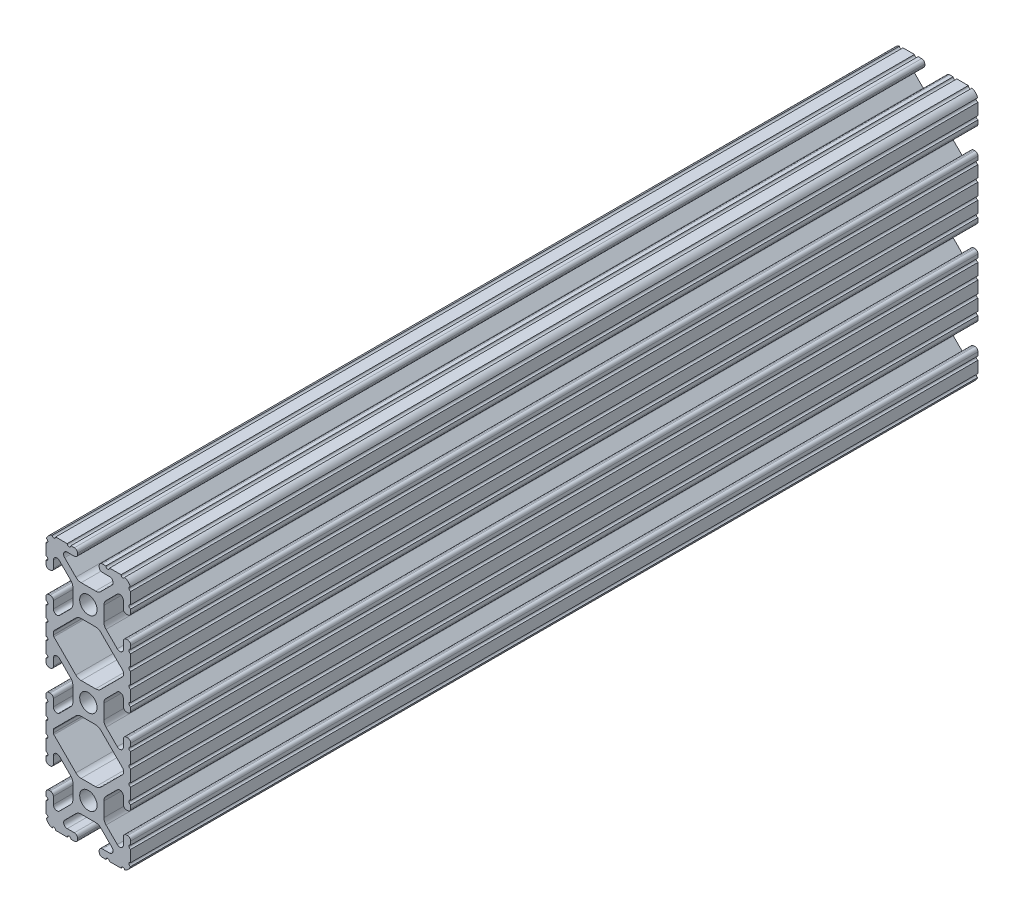
SolidWorks part; units mm, degrees
material "6061-T6 (SS)"
ref_plane "Front Plane" through (0, 0, 0) normal (0, 0, 1) x (1, 0, 0)
ref_plane "Top Plane" through (0, 0, 0) normal (0, 1, 0) x (1, 0, 0)
ref_plane "Right Plane" through (0, 0, 0) normal (1, 0, 0) x (0, 0, -1)
sketch "Sketch2" plane through (0, 0, 0) normal (0, 0, 1) x (1, 0, 0)
  line L0 (0, 38.1) -> (0, -38.1) construction
  line L1 (-12.7, 0) -> (12.7, 0) construction
  line L2 (3.2512, -38.1) -> (12.7, -38.1)
  line L3 (12.7, -38.1) -> (12.7, -28.6512)
  line L4 (3.2512, -38.1) -> (3.2512, -35.8902)
  line L5 (3.2512, -35.8902) -> (8.9276, -35.8902)
  line L6 (8.9276, -35.8902) -> (3.0856, -30.0482)
  line L7 (0, -25.4) -> (12.7, -38.1) construction
  line L8 (12.7, -28.6512) -> (10.4902, -28.6512)
  line L9 (10.4902, -28.6512) -> (10.4902, -34.3276)
  line L10 (10.4902, -34.3276) -> (4.6482, -28.4856)
  circle A0 centre (0, -25.4) radius 2.6035
  arc A1 (6.3485, -35.8902) -> (7.1039, -34.0665) centre (6.3485, -34.8219) ccw construction
  point P8 (0, -30.0482)
  dimension "Center Hole Diameter" = 5.207
  dimension "Rail Height" = 76.2
  dimension "Rail Width" = 25.4
  dimension "T-Slot Width" = 6.5024
  dimension "Slot Inner Width" = 14.8336
  dimension "Thickness" = 2.2098
  dimension "Slot Depth" = 5.842
  dimension "D1" = 2.2098
  dimension "D2" = 50.8
sketch "Sketch3" plane through (0, 0, 0) normal (1, 0, 0) x (0, 0, -1)
  line L0 (-152.4, -38.1) -> (152.4, -38.1) construction
  line L1 (-127, 0) -> (127, 0) construction
  dimension "D1" = 25.4
  dimension "Length" = 304.8
sketch "Sketch4" plane through (0, 0, 0) normal (0, 0, 1) x (1, 0, 0)
  line L0 (4.1904, -38.1) -> (10.1173, -38.1)
  line L1 (3.2512, -38.1) -> (12.7, -38.1) construction
  line L2 (3.2512, -38.1) -> (3.2512, -35.8902) construction
  line L3 (3.2512, -35.8902) -> (8.9276, -35.8902) construction
  line L4 (3.2512, -36.8294) -> (3.2512, -37.1608)
  line L5 (4.1904, -35.8902) -> (6.3485, -35.8902)
  line L6 (0, -30.0482) -> (2.164, -30.0482)
  line L7 (8.9276, -35.8902) -> (3.0856, -30.0482) construction
  line L8 (3.7373, -30.6999) -> (7.1039, -34.0665)
  line L9 (12.7, -38.1) -> (12.7, -28.6512) construction
  line L10 (10.4902, -34.3276) -> (4.6482, -28.4856) construction
  line L11 (10.4902, -28.6512) -> (10.4902, -34.3276) construction
  line L12 (10.4902, -31.7485) -> (10.4902, -29.5904)
  line L13 (12.7, -28.6512) -> (10.4902, -28.6512) construction
  line L14 (11.4294, -28.6512) -> (11.7608, -28.6512)
  line L15 (12.7, -29.5904) -> (12.7, -35.5173)
  line L16 (8.6665, -32.5039) -> (5.2999, -29.1373)
  line L17 (4.6482, -25.4) -> (4.6482, -27.564)
  line L19 (0, -30.0482) -> (0, -28.0035)
  line L20 (0, 38.1) -> (0, -38.1) construction
  line L21 (4.6482, -25.4) -> (2.6035, -25.4)
  arc A0 (3.2512, -37.1608) -> (4.1904, -38.1) centre (4.1904, -37.1608) ccw
  circle A1 centre (0, -25.4) radius 2.6035 construction
  arc A2 (3.2512, -36.8294) -> (4.1904, -35.8902) centre (4.1904, -36.8294) cw
  arc A3 (6.3485, -35.8902) -> (7.1039, -34.0665) centre (6.3485, -34.8219) ccw
  arc A4 (2.164, -30.0482) -> (3.7373, -30.6999) centre (2.164, -32.2732) cw
  arc A5 (10.1173, -38.1) -> (12.7, -35.5173) centre (10.1173, -35.5173) ccw
  arc A6 (8.6665, -32.5039) -> (10.4902, -31.7485) centre (9.4219, -31.7485) ccw
  arc A7 (10.4902, -29.5904) -> (11.4294, -28.6512) centre (11.4294, -29.5904) cw
  arc A8 (11.7608, -28.6512) -> (12.7, -29.5904) centre (11.7608, -29.5904) cw
  arc A9 (5.2999, -29.1373) -> (4.6482, -27.564) centre (6.8732, -27.564) cw
  arc A11 (0, -28.0035) -> (2.6035, -25.4) centre (0, -25.4) ccw
  dimension "D1" = 2.5827
  dimension "D2" = 2.225
  dimension "D3" = 0.9392
extrude "Boss-Extrude1" add sketch "Sketch4" along normal mid plane 254
sketch "Sketch5" plane through (0, 0, 0) normal (0, 0, 1) x (1, 0, 0)
  line L0 (3.2512, -38.1) -> (12.7, -38.1) construction
  line L1 (4.1904, -35.8902) -> (6.3485, -35.8902) construction
  line L3 (0, -25.4) -> (12.7, -38.1) construction
  line L4 (6.3485, -35.8902) -> (6.3485, -38.1) construction
  line L5 (8.9276, -35.8902) -> (3.0856, -30.0482) construction
  circle A0 centre (10.3562, -38.1) radius 0.5524
  circle A1 centre (5.796, -38.1) radius 0.5524
  circle A2 centre (12.7, -35.7562) radius 0.5525
  circle A3 centre (12.7, -31.196) radius 0.5525
  point P10 (5.2694, -35.8902)
  point P12 (9.4219, -31.7485)
  dimension "D1" = 1.1049
extrude "Cut-Extrude1" cut sketch "Sketch5" against normal through all both and the other way through all
mirror "Mirror1" about plane through (4.6482, -25.4, 127) normal (0, -1, 0) of bodies 137 134
sketch "Sketch6" plane through (0, 0, 0) normal (0, 0, 1) x (1, 0, 0)
  line L0 (12.7, -14.4914) -> (12.7, -12.7)
  line L1 (12.7, -12.7) -> (9.8037, -12.7)
  line L3 (9.8037, -12.7) -> (9.8037, -15.5963)
  line L4 (9.8037, -15.5963) -> (12.7, -15.5963)
  line L5 (6.3485, -12.7) -> (9.8037, -12.7) construction
  circle A0 centre (12.7, -15.0438) radius 0.5525 construction
  arc A1 (12.7, -14.4914) -> (12.7, -15.5963) centre (12.7, -15.0438) ccw
  arc A4 (9.8037, -12.7) -> (10.8954, -12.82) centre (10.3562, -12.7) ccw construction
extrude "Boss-Extrude2" add sketch "Sketch6" along normal mid plane 254
sketch "Sketch7" plane through (0, 0, 0) normal (0, 0, 1) x (1, 0, 0)
  line L0 (5.4206, -18.4168) -> (10.3284, -13.509)
  line L1 (3.7373, -20.1001) -> (7.1039, -16.7335) construction
  line L2 (10.4902, -13.1184) -> (10.4902, -12.7)
  line L3 (0, -12.7) -> (10.4902, -12.7)
  line L5 (0, -12.7) -> (5.4206, -18.4168)
  line L7 (0, 38.1) -> (0, -38.1) construction
  line L8 (6.3485, -12.7) -> (12.7, -12.7) construction
  arc A0 (10.3284, -13.509) -> (10.4902, -13.1184) centre (9.9377, -13.1184) ccw
  arc A3 (12.7, -14.4914) -> (12.7, -15.5963) centre (12.7, -15.0438) ccw construction
extrude "Cut-Extrude2" cut sketch "Sketch7" against normal through all both and the other way through all
mirror "Mirror2" about plane through (4.1904, -12.7, 127) normal (0, -1, 0) of bodies 139 135
other "SurfaceCut1"
mirror "Mirror3" about plane through (0, 0, 0) normal (1, 0, 0) of bodies 142 136
mirror "Mirror4" about plane through (0, 0, 0) normal (0, 1, 0) of bodies 140
equation "\"D1@Sketch2\"= \"Thickness@Sketch2\""
equation "\"D2@Sketch4\"=\"Slot Inner Width@Sketch2\"*0.15"
equation "\"D1@Sketch4\"=\"D3@Sketch4\"*2.75"
equation "\"D3@Sketch4\"=\"Thickness@Sketch2\"*0.425"
equation "\"D1@Sketch5\"= \"Thickness@Sketch2\" * 0.5"
equation "\"D1@Boss-Extrude2\" = \"altitude_horizontal_rail_length\""
equation "\"azimuth_horizontal_rail_length\"=(\"altitude_horizontal_rail_length\"+6in-0.29in)"
equation "\"azimuth_vertictal_rail_length\"=6in"
equation "\"wall_screw_clearance_diameter\"=4.3mm"
equation "\"altitude_horizontal_rail_length\"=10in"
equation "\"altitude_vertictal_rail_length\"=12in"
equation "\"D1@Boss-Extrude1\"=\"altitude_horizontal_rail_length\""
